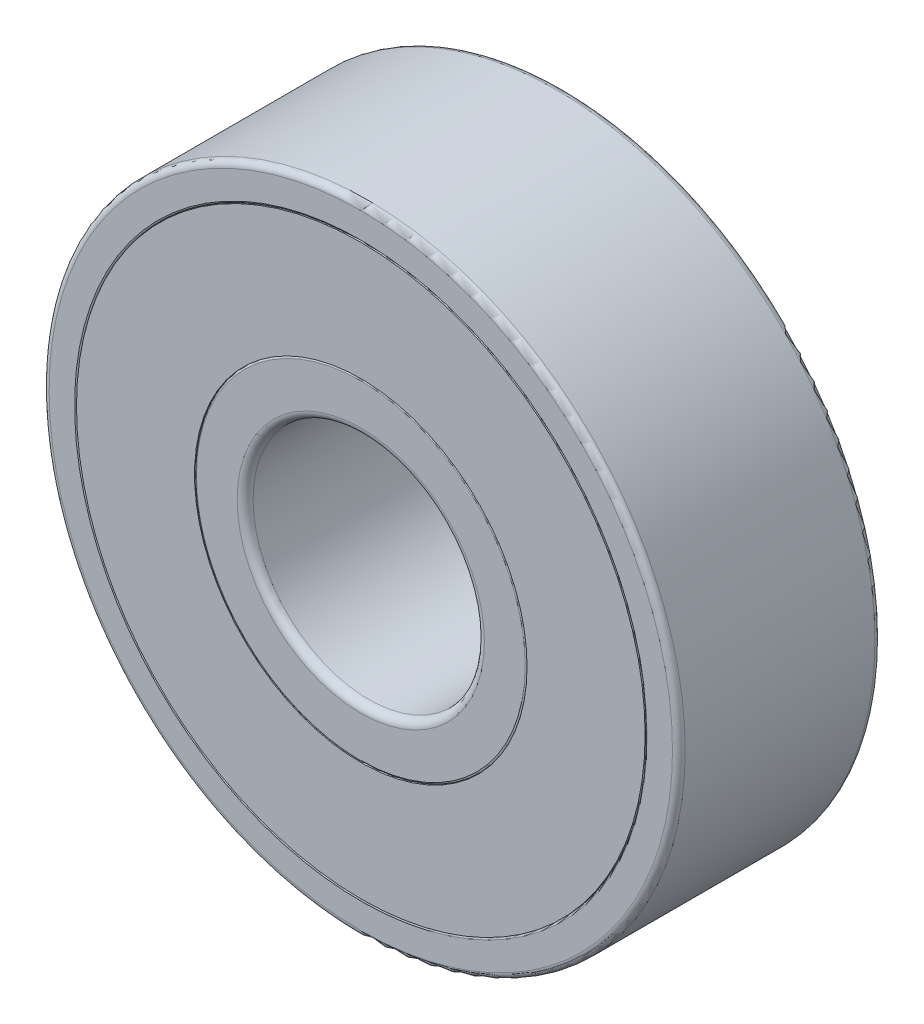
SolidWorks part; units mm, degrees
material "Stainless Steel (ferritic)"
ref_plane "Front Plane" through (0, 0, 0) normal (0, 0, 1) x (1, 0, 0)
ref_plane "Top Plane" through (0, 0, 0) normal (0, 1, 0) x (1, 0, 0)
ref_plane "Right Plane" through (0, 0, 0) normal (1, 0, 0) x (0, 0, -1)
sketch "Sketch1" plane through (0, 0, 0) normal (0, 0, 1) x (1, 0, 0)
  line L0 (0, 11) -> (0, 7.5) construction
  line L1 (0, 7.5) -> (0, 4) construction
  line L2 (0, 11) -> (0, 9.8333) construction
  line L3 (0, 9.8333) -> (0, 8.6667) construction
  line L4 (0, 8.6667) -> (0, 7.5) construction
  circle A0 centre (0, 0) radius 4
  circle A1 centre (0, 0) radius 11
  circle A2 centre (0, 0) radius 9.8333 construction
  circle A4 centre (0, 0) radius 5.75 construction
  point P5 (0, 5.75)
  dimension "OD" = 22
  dimension "ID" = 8
sketch "Sketch2" plane through (0, 0, 0) normal (1, 0, 0) x (0, 0, -1)
  line L0 (-3.5, -11) -> (3.5, -11) construction
  point P2 (0, -11)
  dimension "Width" = 7
sketch "Sketch3" plane through (0, 0, 0) normal (1, 0, 0) x (0, 0, -1)
  line L0 (-3.5, -11) -> (3.5, -11)
  line L1 (3.5, -11) -> (3.5, -9.8333)
  line L2 (3.5, -9.8333) -> (-3.5, -9.8333)
  line L3 (-3.5, -9.8333) -> (-3.5, -11)
  line L6 (-3.5, -4) -> (3.5, -4)
  line L9 (-3.5, -5.75) -> (3.5, -5.75)
  line L12 (-3.5, -5.75) -> (-3.5, -4)
  line L13 (3.5, -5.75) -> (3.5, -4)
  line L14 (-3.5, 0) -> (3.5, 0) construction
  point P6 (0, -9.8333)
  point P7 (0, -5.75)
  point P8 (0, -4)
  dimension "D1" = 4.0833
revolve "Revolve1" add sketch "Sketch3" angle 360 about L14
sketch "Sketch4" plane through (0, 0, 0) normal (1, 0, 0) x (0, 0, -1)
  line L0 (0, 11) -> (0, -11) construction
  line L1 (-3.5, -5.75) -> (-3.5, -9.8333) construction
  circle A0 centre (0, -7.7917) radius 2.45
  point P8 (-3.5, -7.7917)
  dimension "D1" = 4.9
revolve "Cut-Revolve1" cut sketch "Sketch4" angle 360 about L14
sketch "Sketch5" plane through (0, 0, 0) normal (1, 0, 0) x (0, 0, -1)
  line L0 (0, -5.3417) -> (0, -10.2417)
  line L1 (0, 11) -> (0, -11) construction
  circle A0 centre (0, -7.7917) radius 2.45 construction
  arc A1 (0, -5.3417) -> (0, -10.2417) centre (0, -7.7917) cw
revolve "Revolve2" add sketch "Sketch5" angle 360 about L0
pattern_circular "CirPattern1" count 7 over 360 about axis through (0, 0, 0) along (0, 0, 1) of bodies 138
fillet "Fillet1" radius 0.22 2 edges at (11, 0, -3.5) (11, 0, 3.5)
fillet "Fillet2" radius 0.275 2 edges at (4, 0, -3.5) (4, 0, 3.5)
fillet "Fillet3" radius 0.066 2 edges at (9.8333, 0, -3.5) (9.8333, 0, 3.5)
fillet "Fillet4" radius 0.066 2 edges at (5.75, 0, -3.5) (5.75, 0, 3.5)
sketch "Sketch6" plane through (0, 0, 0) normal (0, 0, 1) x (1, 0, 0)
  circle A0 centre (0, 0) radius 9.8333 construction
  circle A1 centre (0, 0) radius 9.8333
  circle A2 centre (0, 0) radius 5.75 construction
  circle A3 centre (0, 0) radius 5.75
extrude "Boss-Extrude2" add sketch "Sketch6" along normal mid plane 7 separate body
equation "\"D1@Sketch4\"=\"D1@Sketch3\"*1.2"
equation "\"D1@Fillet1\"=\"OD@Sketch1\"*0.01"
equation "\"D1@Fillet2\"=\"D1@Fillet1\"*1.25"
equation "\"D1@Fillet3\"=\"D1@Fillet1\"*0.3"
equation "\"D1@Fillet4\"=\"D1@Fillet3\""
equation "\"D1@Boss-Extrude2\"=\"width@sketch2\""
